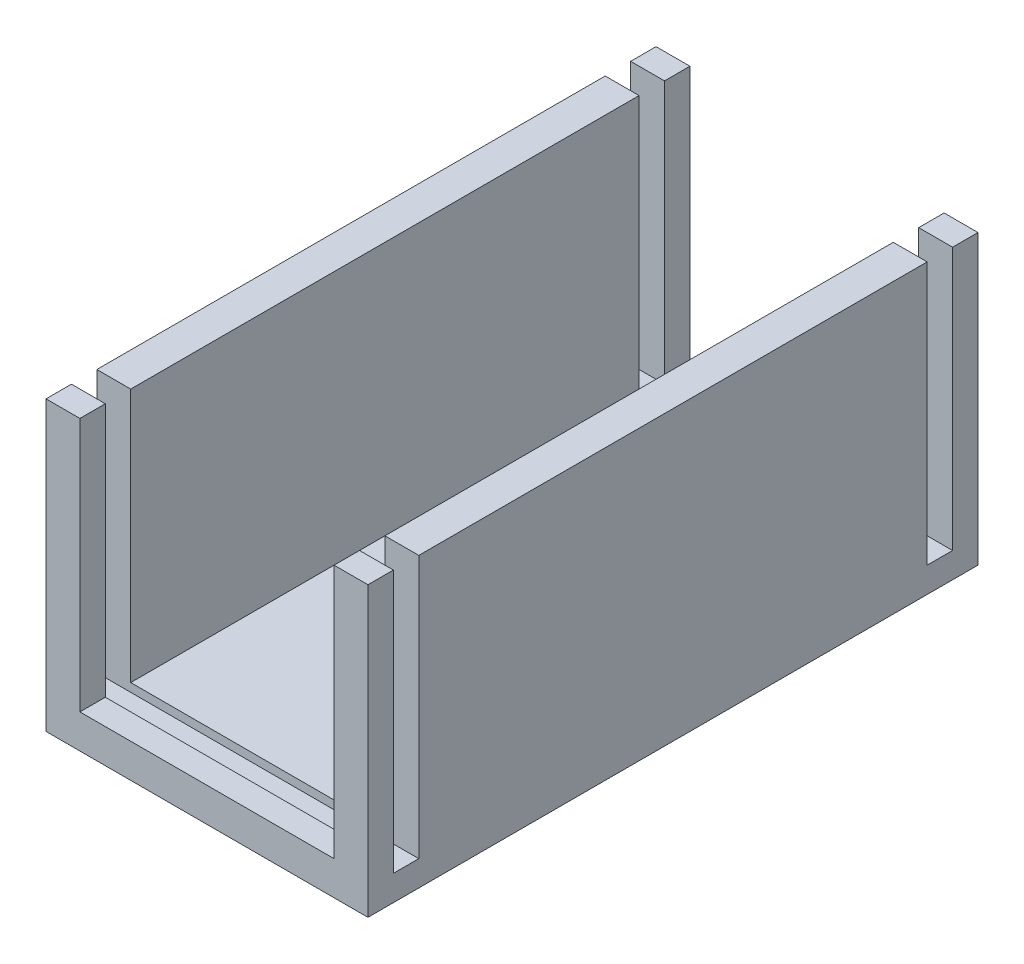
SolidWorks part; units mm, degrees
ref_plane "Front Plane" through (0, 0, 0) normal (0, 0, 1) x (1, 0, 0)
ref_plane "Top Plane" through (0, 0, 0) normal (0, 1, 0) x (1, 0, 0)
ref_plane "Right Plane" through (0, 0, 0) normal (1, 0, 0) x (0, 0, -1)
sketch "Sketch1" plane through (0, 0, 0) normal (0, 0, 1) x (1, 0, 0)
  line L1 (9.5, -8.5) -> (-9.5, -8.5)
  line L2 (9.5, -8.5) -> (9.5, 8.5)
  line L3 (9.5, 8.5) -> (-9.5, 8.5)
  line L4 (-9.5, -8.5) -> (-9.5, 8.5)
  line L5 (9.5, -8.5) -> (-9.5, 8.5) construction
  line L6 (9.5, 8.5) -> (-9.5, -8.5) construction
  point P0 (0, 0)
  dimension "D1" = 19
  dimension "D2" = 17
extrude "Boss-Extrude1" add sketch "Sketch1" along normal blind 36
sketch "Sketch2" plane through (0, 8.5, 0) normal (0, 1, 0) x (1, 0, 0)
  line L0 (-9.5, -36) -> (-9.5, 0) construction
  line L1 (7.5, -36) -> (-7.5, -36)
  line L2 (7.5, -36) -> (7.5, 0)
  line L3 (7.5, 0) -> (-7.5, 0)
  line L4 (-7.5, -36) -> (-7.5, 0)
  line L5 (7.5, -36) -> (-7.5, 0) construction
  line L6 (7.5, 0) -> (-7.5, -36) construction
  line L7 (9.5, -36) -> (9.5, 0) construction
  line L9 (9.5, 0) -> (-9.5, 0) construction
  line L10 (9.5, -36) -> (-9.5, -36) construction
  point P0 (0, -18)
  dimension "D1" = 2
  dimension "D2" = 2
extrude "Cut-Extrude1" cut sketch "Sketch2" against normal blind 15
sketch "Sketch3" plane through (0, 8.5, 0) normal (0, 1, 0) x (1, 0, 0)
  line L0 (-9.5, -36) -> (-9.5, 0) construction
  line L1 (-9.5, -34.5) -> (9.5, -34.5)
  line L2 (-9.5, -34.5) -> (-9.5, -33)
  line L3 (-9.5, -33) -> (9.5, -33)
  line L4 (9.5, -34.5) -> (9.5, -33)
  line L5 (9.5, -36) -> (9.5, 0) construction
  line L6 (-7.5, -36) -> (-9.5, -36) construction
  line L7 (-7.5, 0) -> (-9.5, 0) construction
  line L8 (-9.5, -1.5) -> (9.5, -1.5)
  line L9 (-9.5, -1.5) -> (-9.5, -3)
  line L10 (-9.5, -3) -> (9.5, -3)
  line L11 (9.5, -1.5) -> (9.5, -3)
  dimension "D1" = 1.5
  dimension "D2" = 1.5
  dimension "D3" = 1.5
  dimension "D4" = 1.5
extrude "Cut-Extrude2" cut sketch "Sketch3" against normal blind 15.5
equation "\"D2@Sketch3\"=\"D4@Sketch3\""
equation "\"D1@Sketch3\"=\"D3@Sketch3\""
